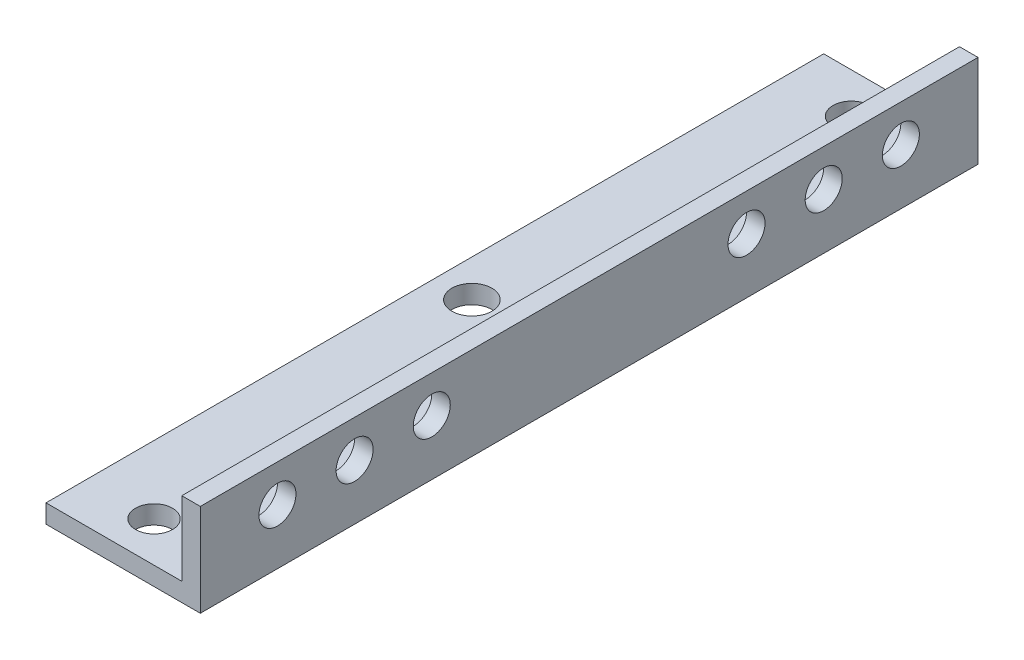
SolidWorks part; units mm, degrees
ref_plane "Alzado" through (0, 0, 0) normal (0, 0, 1) x (1, 0, 0)
ref_plane "Planta" through (0, 0, 0) normal (0, 1, 0) x (1, 0, 0)
ref_plane "Vista lateral" through (0, 0, 0) normal (1, 0, 0) x (0, 0, -1)
sketch "Croquis1" plane through (0, 0, 0) normal (0, 0, 1) x (1, 0, 0)
  line L0 (0, 0) -> (3, 0)
  line L1 (3, 0) -> (3, -15)
  line L2 (3, -15) -> (-22, -15)
  line L3 (-22, -15) -> (-22, -12)
  line L4 (-22, -12) -> (0, -12)
  line L5 (0, -12) -> (0, 0)
  dimension "D1" = 3
  dimension "D2" = 3
  dimension "D3" = 15
  dimension "D4" = 25
extrude "Saliente-Extruir1" add sketch "Croquis1" along normal blind 126
sketch "Croquis2" plane through (3, 0, 0) normal (1, 0, 0) x (0, 0, -1)
  line L2 (-63, -15) -> (-63, 0) construction
  line L3 (-126, -15) -> (0, -15) construction
  line L4 (-126, 0) -> (0, 0) construction
  circle A0 centre (-113.5, -6) radius 3
  circle A1 centre (-101, -6) radius 3
  circle A2 centre (-88.5, -6) radius 3
  circle A6 centre (-12.5, -6) radius 3
  circle A7 centre (-25, -6) radius 3
  circle A8 centre (-37.5, -6) radius 3
  dimension "D2" = 6
  dimension "D3" = 6
  dimension "D1" = 6
  dimension "D4" = 12.5
  dimension "D5" = 12.5
extrude "Cortar-Extruir3" cut sketch "Croquis2" against normal mid plane 126
sketch "Croquis3" plane through (0, -12, 0) normal (0, 1, 0) x (1, 0, 0)
  line L0 (-11, 0) -> (-11, -6.5) construction
  line L1 (0, 0) -> (-22, 0) construction
  line L2 (-11, -6.5) -> (-22, -6.5) construction
  line L3 (-22, -126) -> (-22, 0) construction
  line L4 (-22, -63) -> (0, -63) construction
  line L5 (0, -126) -> (0, 0) construction
  circle A0 centre (-11, -6.5) radius 3
  circle A1 centre (-11, -119.5) radius 3
  circle A2 centre (-16, -63) radius 3.2434
  circle A3 centre (-6, -63) radius 3.3511
  dimension "D3" = 6
  dimension "D1" = 11
  dimension "D2" = 6.5
  dimension "D4" = 10
extrude "Cortar-Extruir4" cut sketch "Croquis3" against normal blind 10
